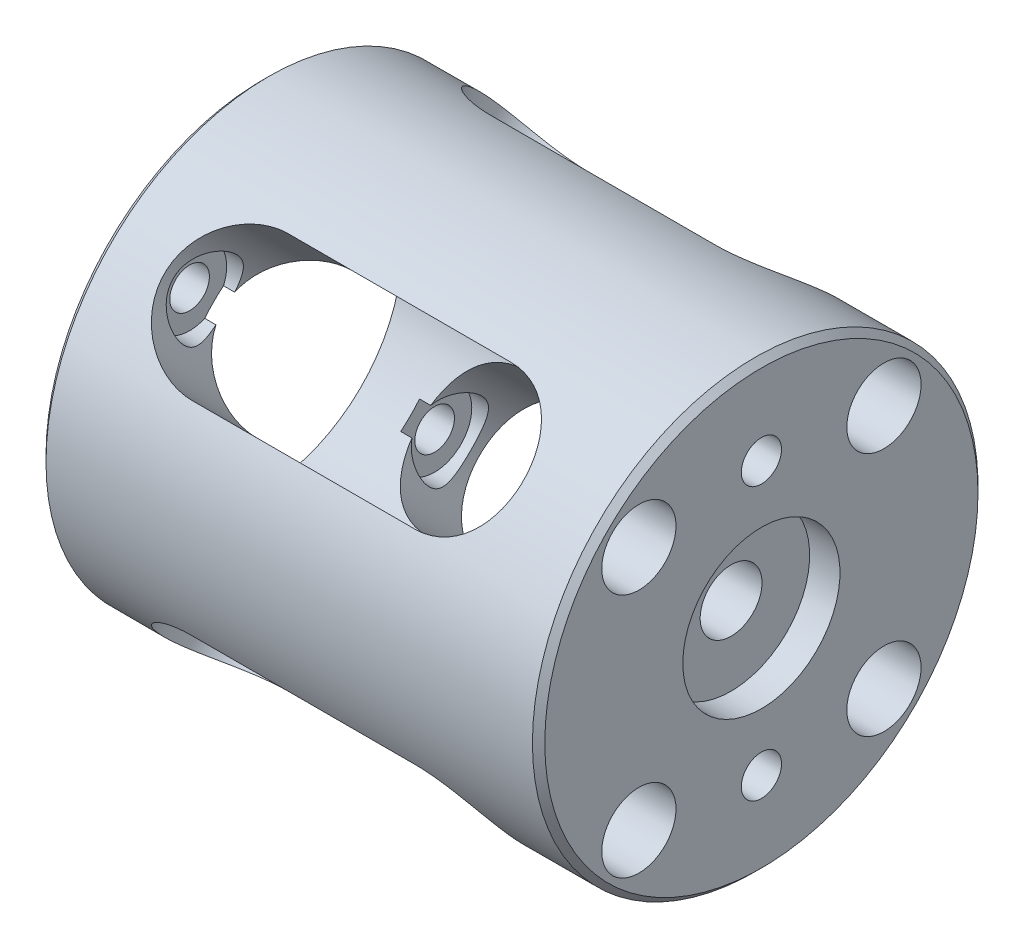
SolidWorks part; units mm, degrees
ref_plane "Front Plane" through (0, 0, 0) normal (0, 0, 1) x (1, 0, 0)
ref_plane "Top Plane" through (0, 0, 0) normal (0, 1, 0) x (1, 0, 0)
ref_plane "Right Plane" through (0, 0, 0) normal (1, 0, 0) x (0, 0, -1)
sketch "Sketch2" plane through (0, 0, 0) normal (0, 1, 0) x (1, 0, 0)
  line L0 (-68.5873, 0) -> (139.3492, 0) construction
  line L1 (-40.3, 18) -> (-40.3, 11.25)
  line L2 (0, 6.35) -> (-2.45, 6.35)
  line L3 (0, 6.35) -> (0, 18)
  line L4 (-2.45, 6.35) -> (-2.45, 2.5)
  line L5 (-2.45, 2.5) -> (-6.3, 2.5)
  line L6 (0, 18) -> (-40.3, 18)
  line L9 (-6.3, 2.5) -> (-6.3, 11.25)
  line L10 (-6.3, 11.25) -> (-40.3, 11.25)
  dimension "D1" = 18
  dimension "D2" = 2.45
  dimension "D3" = 2.5
  dimension "D4" = 6.3
  dimension "D5" = 6.35
  dimension "D6" = 11.25
  dimension "D7" = 34
revolve "Revolve1" add sketch "Sketch2" angle 360 about L0
sketch "Sketch7" plane through (0, 0, 0) normal (1, 0, 0) x (0, 0, -1)
  line L0 (-14.0397, -14.0397) -> (14.9167, 14.9167) construction
  line L1 (-15.1522, 15.1522) -> (16.849, -16.849) construction
  line L2 (-23.7673, 0) -> (22.3348, 0) construction
  circle A0 centre (-9.8995, 9.8995) radius 1.6
  circle A1 centre (9.8995, 9.8995) radius 1.6
  circle A2 centre (9.8995, -9.8995) radius 1.6
  circle A3 centre (-9.8995, -9.8995) radius 1.6
  dimension "D7" = 3.2
  dimension "D8" = 3.2
  dimension "D9" = 3.2
  dimension "D10" = 3.2
  dimension "D1" = 45
  dimension "D2" = 90
  dimension "D3" = 14
  dimension "D4" = 14
  dimension "D5" = 14
  dimension "D6" = 14
extrude "Cut-Extrude1" cut sketch "Sketch7" against normal through all
sketch "Sketch8" plane through (0, 0, 0) normal (1, 0, 0) x (0, 0, -1)
  circle A0 centre (-9.8995, 9.8995) radius 3
  circle A1 centre (9.8995, 9.8995) radius 3
  circle A2 centre (-9.8995, -9.8995) radius 3
  circle A3 centre (9.8995, -9.8995) radius 3
  dimension "D1" = 6
  dimension "D2" = 6
  dimension "D3" = 6
  dimension "D4" = 6
extrude "Cut-Extrude2" cut sketch "Sketch8" against normal blind 36.3
sketch "Sketch9" plane through (-40.3, 0, 0) normal (-1, 0, 0) x (0, 0, 1)
  circle A0 centre (0, 11) radius 1.625
  circle A1 centre (0, -11) radius 1.625
  dimension "D1" = 3.25
  dimension "D2" = 3.25
  dimension "D3" = 11
  dimension "D4" = 22
extrude "Cut-Extrude3" cut sketch "Sketch9" against normal through all
sketch "Sketch10" plane through (-40.3, 0, 0) normal (-1, 0, 0) x (0, 0, 1)
  circle A0 centre (0, 11) radius 2.425
  circle A1 centre (0, -11) radius 2.425
  dimension "D1" = 4.85
  dimension "D2" = 4.85
extrude "Cut-Extrude4" cut sketch "Sketch10" against normal blind 37
chamfer "Chamfer1" distance 0.5 angle 45 2 edges at (0, 0, 18) (-40.3, 0, 18)
sketch "Sketch12" plane through (0, 0, 0) normal (0, 1, 0) x (1, 0, 0)
  line L0 (0, 0) -> (-40.3, 0) construction
  line L1 (-40.3, 17.5) -> (-40.3, -17.5) construction
ref_plane "Plane1" through (0, 0, 0) normal (0, 0.7071, -0.7071) x (-1, 0, 0)
sketch "Sketch13" plane through (0, 0, 0) normal (0, 0.7071, -0.7071) x (-1, 0, 0)
  line L0 (12, 0) -> (30, 0) construction
  line L1 (0, 0) -> (40.3, 0) construction
  line L2 (12, 5.5) -> (30, 5.5)
  line L3 (12, -5.5) -> (30, -5.5)
  line L6 (0, 17.5) -> (0, -17.5) construction
  arc A0 (12, 5.5) -> (12, -5.5) centre (12, 0) ccw
  arc A1 (30, -5.5) -> (30, 5.5) centre (30, 0) ccw
  point P4 (21, 0)
  dimension "D3" = 5.5
  dimension "D1" = 18
  dimension "D2" = 12
extrude "Cut-Extrude5" cut sketch "Sketch13" against normal through all and the other way through all
ref_plane "Plane2" through (0, 0, 0) normal (0, -0.7071, -0.7071) x (-1, 0, 0)
sketch "Sketch14" plane through (0, 0, 0) normal (0, -0.7071, -0.7071) x (-1, 0, 0)
  line L0 (12, 0) -> (30, 0) construction
  line L1 (0, 0) -> (40.3, 0) construction
  line L2 (12, 5.5) -> (30, 5.5)
  line L3 (12, -5.5) -> (30, -5.5)
  line L5 (0, 17.5) -> (0, -17.5) construction
  arc A0 (12, 5.5) -> (12, -5.5) centre (12, 0) ccw
  arc A1 (30, -5.5) -> (30, 5.5) centre (30, 0) ccw
  point P4 (21, 0)
  dimension "D3" = 5.5
  dimension "D1" = 18
  dimension "D2" = 12
extrude "Cut-Extrude6" cut sketch "Sketch14" against normal through all and the other way through all
